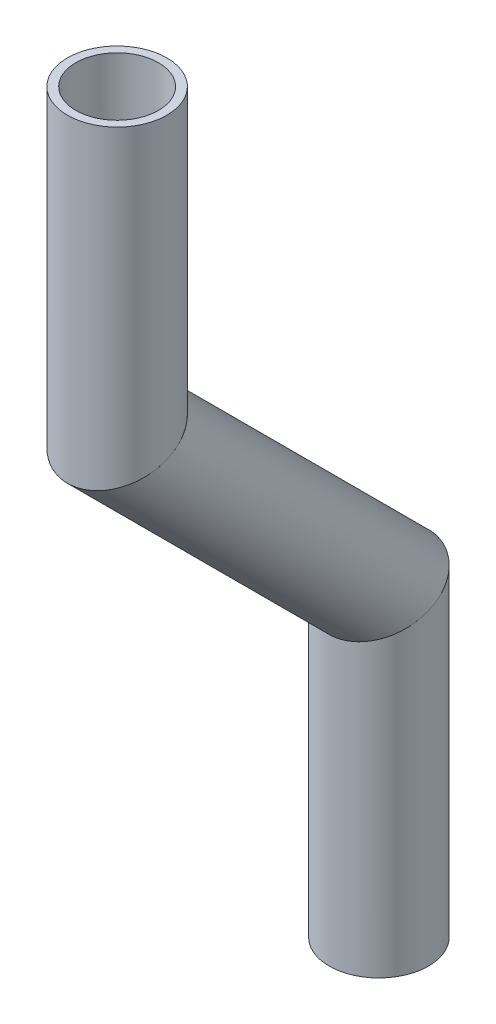
SolidWorks part; units mm, degrees
ref_plane "Front Plane" through (0, 0, 0) normal (0, 0, 1) x (1, 0, 0)
ref_plane "Top Plane" through (0, 0, 0) normal (0, 1, 0) x (1, 0, 0)
ref_plane "Right Plane" through (0, 0, 0) normal (1, 0, 0) x (0, 0, -1)
sketch "Sketch1" plane through (0, 0, 0) normal (1, 0, 0) x (0, 0, -1)
  line L0 (-303.2502, -187.7563) -> (-303.2502, -225.8563)
  line L1 (-303.2502, -225.8563) -> (-269.8103, -259.2962)
  line L2 (-269.8103, -259.2962) -> (-269.8103, -298.6197)
  line L3 (-303.2502, -225.8563) -> (-303.2502, -238.7774) construction
  dimension "D1" = 45
  dimension "D2" = 38.1
  dimension "D3" = 39.3235
other "Pipe 0.5 SCH 40(1)"
ref_plane "Plane1" through (0, -187.7563, 303.2502) normal (0, -1, 0) x (0, 0, -1)
sketch "Sketch11" plane through (0, -187.7563, 303.2502) normal (0, -1, 0) x (0, 0, -1)
  circle A0 centre (0, 0) radius 5.2832
  circle A1 centre (0, 0) radius 6.35
  point P5 (0, 0)
  dimension "In_dia" = 10.5664
  dimension "Out_dia" = 12.7
